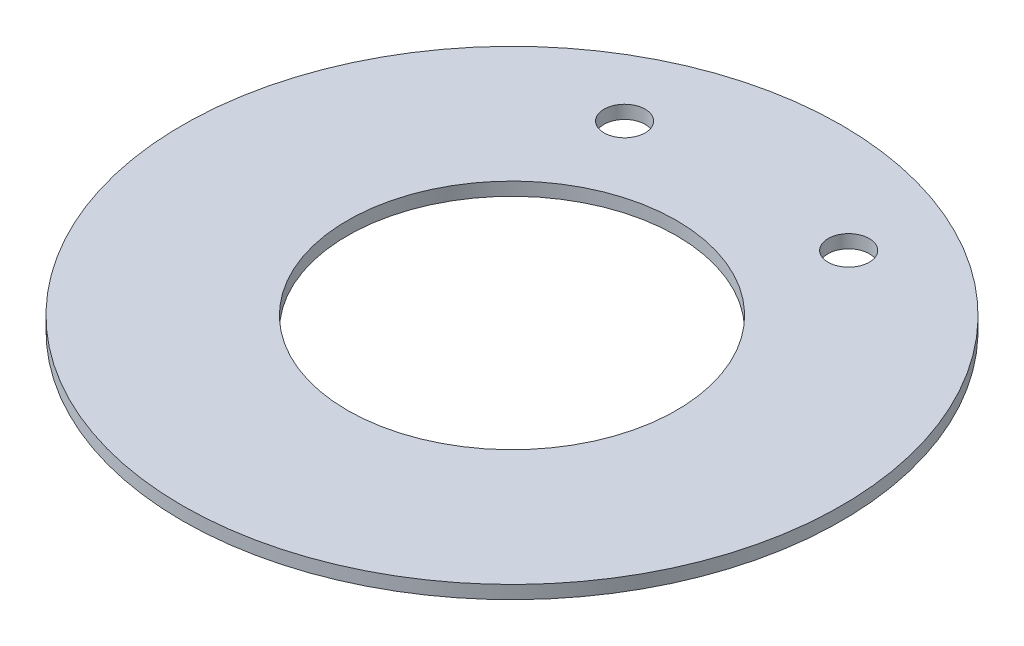
SolidWorks part; units mm, degrees
ref_plane "Front Plane" through (0, 0, 0) normal (0, 0, 1) x (1, 0, 0)
ref_plane "Top Plane" through (0, 0, 0) normal (0, 1, 0) x (1, 0, 0)
ref_plane "Right Plane" through (0, 0, 0) normal (1, 0, 0) x (0, 0, -1)
sketch "Sketch1" plane through (0, 0, 0) normal (0, 1, 0) x (1, 0, 0)
  circle A0 centre (0, 0) radius 39.624
  circle A1 centre (0, 0) radius 79.375
  dimension "D1" = 79.248
  dimension "D2" = 158.75
extrude "Boss-Extrude1" add sketch "Sketch1" along normal blind 3.175
sketch "Sketch2" plane through (0, 3.175, 0) normal (0, 1, 0) x (1, 0, 0)
  line L0 (-26.9875, 54.102) -> (26.9875, 54.102) construction
  line L5 (0, 54.102) -> (0, 0) construction
  circle A0 centre (26.9875, 54.102) radius 4.953
  circle A1 centre (-26.9875, 54.102) radius 4.953
  point P13 (0, 53.2307)
  point P14 (0, 0)
  point P15 (0, 54.1438)
  dimension "D2" = 9.906
  dimension "D1" = 53.975
  dimension "D5" = 54.102
extrude "Cut-Extrude2" cut sketch "Sketch2" against normal through all
